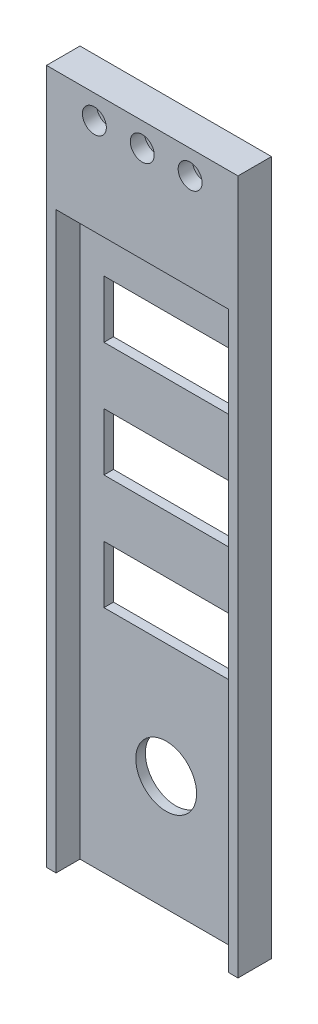
SolidWorks part; units mm, degrees
ref_plane "Front Plane" through (0, 0, 0) normal (0, 0, 1) x (1, 0, 0)
ref_plane "Top Plane" through (0, 0, 0) normal (0, 1, 0) x (1, 0, 0)
ref_plane "Right Plane" through (0, 0, 0) normal (1, 0, 0) x (0, 0, -1)
sketch "Sketch1" plane through (0, 0, 0) normal (0, 0, 1) x (1, 0, 0)
  line L1 (0, 0) -> (40, 0)
  line L2 (0, 0) -> (0, 145.1)
  line L3 (0, 145.1) -> (40, 145.1)
  line L4 (40, 0) -> (40, 145.1)
  dimension "D1" = 145.1
  dimension "D2" = 40
extrude "Boss-Extrude1" add sketch "Sketch1" along normal blind 7 contours L2 L3 L4 L1
sketch "Sketch2" plane through (0, 0, 7) normal (0, 0, 1) x (1, 0, 0)
  line L0 (0, 145.1) -> (40, 145.1) construction
  line L1 (0, 0) -> (0, 145.1) construction
  line L2 (40, 0) -> (40, 145.1) construction
  circle A0 centre (20, 140.1) radius 1.25
  circle A1 centre (10, 140.1) radius 1.25
  circle A2 centre (30, 140.1) radius 1.25
  dimension "D1" = 2.5
  dimension "D2" = 5
  dimension "D3" = 2.5
  dimension "D4" = 2.5
  dimension "D5" = 10
  dimension "D6" = 10
extrude "Cut-Extrude1" cut sketch "Sketch2" against normal blind 7
sketch "Sketch3" plane through (0, 0, 7) normal (0, 0, 1) x (1, 0, 0)
  circle A0 centre (10, 140.1) radius 2.5
  circle A1 centre (20, 140.1) radius 2.5
  circle A2 centre (30, 140.1) radius 2.5
  dimension "D1" = 5
  dimension "D2" = 5
  dimension "D3" = 5
extrude "Cut-Extrude2" cut sketch "Sketch3" against normal blind 3
sketch "Sketch4" plane through (0, 0, 7) normal (0, 0, 1) x (1, 0, 0)
  line L0 (0, 145.1) -> (40, 145.1) construction
  line L1 (0, 0) -> (0, 145.1) construction
  circle A0 centre (20, 24) radius 6.35
  dimension "D1" = 12.7
  dimension "D2" = 121.1
  dimension "D3" = 20
extrude "Cut-Extrude3" cut sketch "Sketch4" against normal through all
sketch "Sketch5" plane through (0, 0, 7) normal (0, 0, 1) x (1, 0, 0)
  line L0 (0, 0) -> (40, 0) construction
  line L1 (2, 0) -> (38, 0)
  line L2 (2, 0) -> (2, 120)
  line L3 (2, 120) -> (38, 120)
  line L4 (38, 0) -> (38, 120)
  line L5 (0, 0) -> (0, 145.1) construction
  line L6 (40, 0) -> (40, 145.1) construction
  dimension "D1" = 2
  dimension "D2" = 2
  dimension "D3" = 120
extrude "Cut-Extrude4" cut sketch "Sketch5" against normal blind 5
sketch "Sketch6" plane through (0, 0, 2) normal (0, 0, 1) x (1, 0, 0)
  line L0 (2, 120) -> (2, 0) construction
  line L1 (7, 108) -> (33, 108)
  line L2 (7, 108) -> (7, 96)
  line L3 (7, 96) -> (33, 96)
  line L4 (33, 108) -> (33, 96)
  line L5 (38, 0) -> (38, 120) construction
  line L6 (38, 120) -> (2, 120) construction
  line L8 (7, 84) -> (33, 84)
  line L9 (7, 84) -> (7, 72)
  line L10 (7, 72) -> (33, 72)
  line L11 (33, 84) -> (33, 72)
  line L12 (7, 60) -> (33, 60)
  line L13 (7, 60) -> (7, 48)
  line L14 (7, 48) -> (33, 48)
  line L15 (33, 60) -> (33, 48)
  dimension "D1" = 5
  dimension "D2" = 5
  dimension "D3" = 12
  dimension "D4" = 12
  dimension "D5" = 12
  dimension "D6" = 12
  dimension "D7" = 12
  dimension "D8" = 12
extrude "Cut-Extrude5" cut sketch "Sketch6" against normal through all
